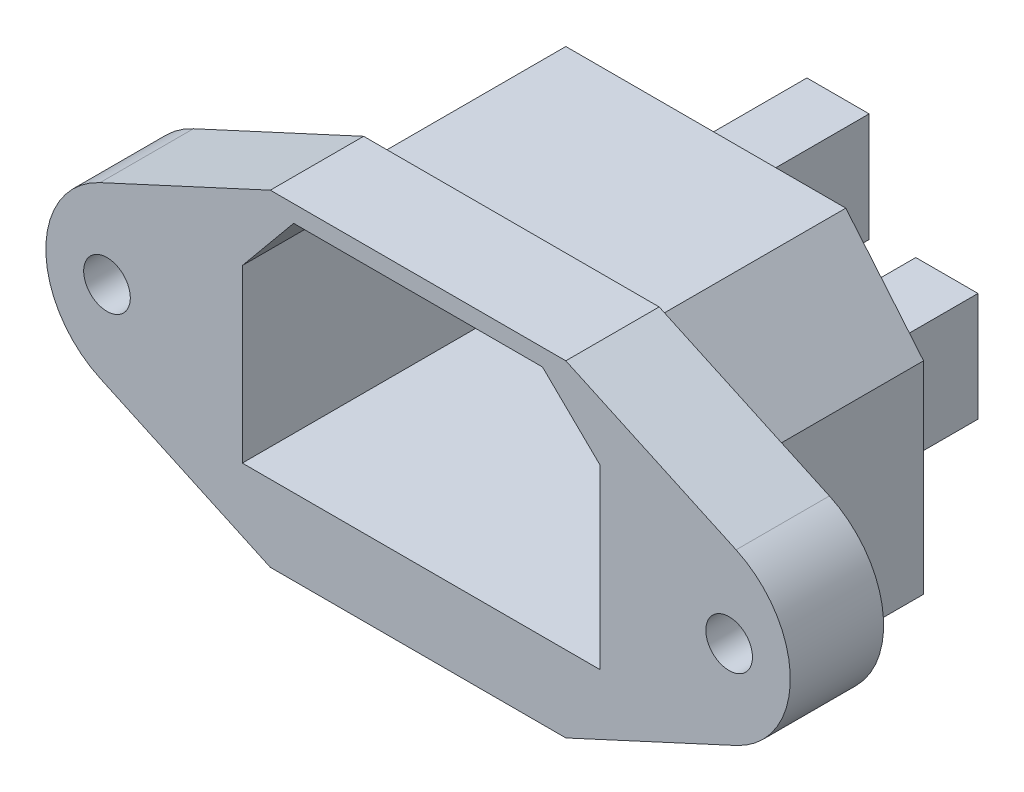
SolidWorks part; units mm, degrees
ref_plane "Plano frontal" through (0, 0, 0) normal (0, 0, 1) x (1, 0, 0)
ref_plane "Plano superior" through (0, 0, 0) normal (0, 1, 0) x (1, 0, 0)
ref_plane "Plano direito" through (0, 0, 0) normal (1, 0, 0) x (0, 0, -1)
sketch "Esboço1" plane through (0, 0, 0) normal (0, 0, 1) x (1, 0, 0)
  line L0 (0, -12.6422) -> (0, 12.5) construction
  line L1 (-9, 12.5) -> (9, 12.5)
  line L2 (14, -6.5) -> (-14, -6.5)
  line L3 (14, -6.5) -> (14, 6.5)
  line L5 (-14, -6.5) -> (-14, 6.5)
  line L6 (14, -6.5) -> (-14, 6.5) construction
  line L7 (14, 6.5) -> (-14, -6.5) construction
  line L8 (-14, 6.5) -> (-9, 12.5)
  line L9 (9, 12.5) -> (14, 6.5)
  point P3 (0, 0)
  point P10 (0, 12.5)
  dimension "D1" = 28
  dimension "D2" = 13
  dimension "D3" = 18
  dimension "D4" = 19
extrude "Ressalto-extrusão1" add sketch "Esboço1" along normal blind 12.5
sketch "Esboço2" plane through (0, 0, 0) normal (0, 0, -1) x (-1, 0, 0)
  line L0 (0, -8.0192) -> (0, 14.3827) construction
  line L1 (-15.904, 0) -> (16.7219, 0) construction
  line L3 (-5, -3.5) -> (-9, -3.5)
  line L4 (-5, -3.5) -> (-5, 3.5)
  line L5 (-5, 3.5) -> (-9, 3.5)
  line L6 (-9, -3.5) -> (-9, 3.5)
  line L7 (-5, -3.5) -> (-9, 3.5) construction
  line L8 (-5, 3.5) -> (-9, -3.5) construction
  line L9 (-14, -6.5) -> (-14, 6.5) construction
  line L10 (-14.6771, 6.5) -> (15.1315, 6.5) construction
  line L11 (2, 3) -> (-2, 3)
  line L12 (2, 3) -> (2, 10)
  line L13 (2, 10) -> (-2, 10)
  line L14 (-2, 3) -> (-2, 10)
  line L15 (2, 3) -> (-2, 10) construction
  line L16 (2, 10) -> (-2, 3) construction
  line L17 (5, 3.5) -> (9, 3.5)
  line L18 (9, -3.5) -> (9, 3.5)
  line L19 (5, -3.5) -> (9, -3.5)
  line L20 (5, -3.5) -> (5, 3.5)
  point P5 (-7, 0)
  point P10 (0, 6.5)
  dimension "D1" = 4
  dimension "D2" = 7
  dimension "D3" = 7
extrude "Ressalto-extrusão2" add sketch "Esboço2" along normal blind 8.5
sketch "Esboço3" plane through (0, 0, 12.5) normal (0, 0, 1) x (1, 0, 0)
  line L0 (0, -8.9734) -> (0, 13.9283) construction
  line L1 (-9.5, -7.5) -> (9.5, -7.5)
  line L2 (-14, -6.5) -> (14, -6.5) construction
  line L4 (-9.5, 13.5) -> (9.5, 13.5)
  line L9 (16, -4.5) -> (-16, 10.5) construction
  line L10 (16, 10.5) -> (-16, -4.5) construction
  line L11 (-9.5, 13.5) -> (-32.25, 3)
  line L12 (9.5, 13.5) -> (32.25, 3)
  line L13 (18.7317, 3) -> (-20.1953, 3) construction
  line L14 (9.5, -7.5) -> (32.25, 3)
  line L15 (-9.5, -7.5) -> (-32.25, 3)
  point P3 (0, 3)
  point P6 (0, 3)
  point P13 (0, 13.5)
  dimension "D1" = 9.5
  dimension "D2" = 32
  dimension "D3" = 15
  dimension "D5" = 19
extrude "Ressalto-extrusão3" add sketch "Esboço3" along normal blind 6
sketch "Esboço4" plane through (0, 0, 18.5) normal (0, 0, 1) x (1, 0, 0)
  line L0 (0, 15.4598) -> (0, -11.8073) construction
  line L1 (-34.8649, 3) -> (42.7887, 3) construction
  circle A0 centre (-20, 3) radius 1.5
  circle A1 centre (20, 3) radius 1.5
  dimension "D1" = 3
  dimension "D2" = 20
extrude "Corte-extrusão1" cut sketch "Esboço4" against normal blind 6
fillet "Filete1" radius 6 2 edges at (32.25, 3, 15.5) (-32.25, 3, 15.5)
sketch "Esboço5" plane through (0, 0, 18.5) normal (0, 0, 1) x (1, 0, 0)
  line L0 (0, 16.1749) -> (0, -15.2807) construction
  line L1 (-33.5526, 3) -> (33.0968, 3) construction
  line L2 (-8, 12.4043) -> (8, 12.4043)
  line L3 (11.7, -2.5957) -> (-11.3, -2.5957)
  line L4 (11.7, -2.5957) -> (11.7, 8.7938)
  line L6 (-11.3, -2.5957) -> (-11.3, 8.4043)
  line L7 (11.7, -2.5957) -> (-11.3, 8.4043) construction
  line L8 (11.7, 8.7938) -> (-11.3, -2.5957) construction
  line L9 (-8, 12.4043) -> (-11.3, 8.4043)
  line L10 (8, 12.4043) -> (11.7, 8.7938)
  point P6 (0, 3)
  point P13 (0, 12.4043)
  dimension "D1" = 11
  dimension "D2" = 23
  dimension "D3" = 16
  dimension "D4" = 15
extrude "Corte-extrusão2" cut sketch "Esboço5" against normal blind 16.5
